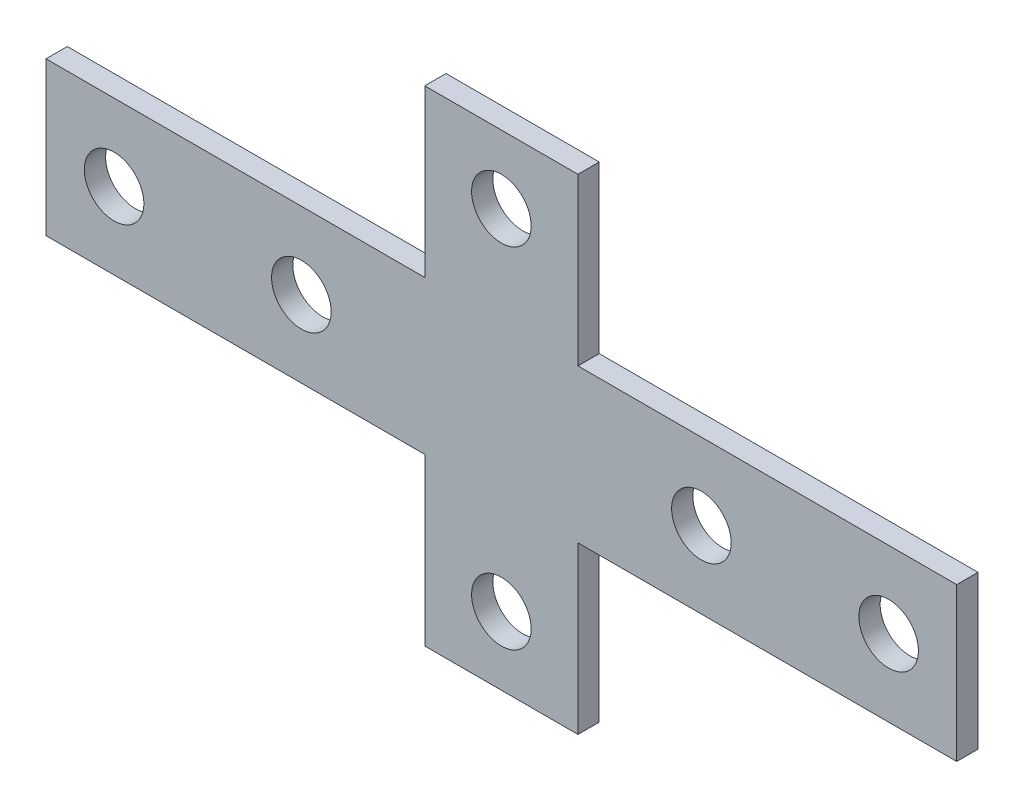
SolidWorks part; units mm, degrees
ref_plane "Спереди" through (0, 0, 0) normal (0, 0, 1) x (1, 0, 0)
ref_plane "Сверху" through (0, 0, 0) normal (0, 1, 0) x (1, 0, 0)
ref_plane "Справа" through (0, 0, 0) normal (1, 0, 0) x (0, 0, -1)
sketch "Эскиз1" plane through (0, 0, 0) normal (0, 0, 1) x (1, 0, 0)
  line L0 (9, -9) -> (53.5, -9)
  line L1 (-53.5, 9) -> (-9, 9)
  line L2 (-53.5, 9) -> (-53.5, -9)
  line L3 (-53.5, -9) -> (-9, -9)
  line L4 (53.5, 9) -> (53.5, -9)
  line L5 (-53.5, 9) -> (53.5, -9) construction
  line L6 (-53.5, -9) -> (53.5, 9) construction
  line L7 (-9, -28.5) -> (9, -28.5)
  line L8 (-9, -28.5) -> (-9, -9)
  line L9 (-9, 28.5) -> (9, 28.5)
  line L10 (9, -28.5) -> (9, -9)
  line L11 (-9, -28.5) -> (9, 28.5) construction
  line L12 (-9, 28.5) -> (9, -28.5) construction
  line L13 (9, 9) -> (53.5, 9)
  line L14 (-9, 9) -> (-9, 28.5)
  line L15 (9, 9) -> (9, 28.5)
  line L16 (0, 20.5) -> (0, -20.5) construction
  line L17 (0, 20.5) -> (0, 28.5) construction
  line L18 (-45.5, 0) -> (-53.5, 0) construction
  circle A0 centre (0, 20.5) radius 3.5
  circle A1 centre (0, -20.5) radius 3.5
  circle A2 centre (-45.5, 0) radius 3.5
  circle A3 centre (-23.5, 0) radius 3.5
  circle A4 centre (23.5, 0) radius 3.5
  circle A5 centre (45.5, 0) radius 3.5
  point P0 (0, 0)
  point P6 (0, 0)
  dimension "D4" = 8
  dimension "D5" = 7
  dimension "D6" = 22
  dimension "D1" = 107
  dimension "D2" = 57
  dimension "D3" = 18
extrude "Бобышка-Вытянуть1" add sketch "Эскиз1" along normal blind 2.5
